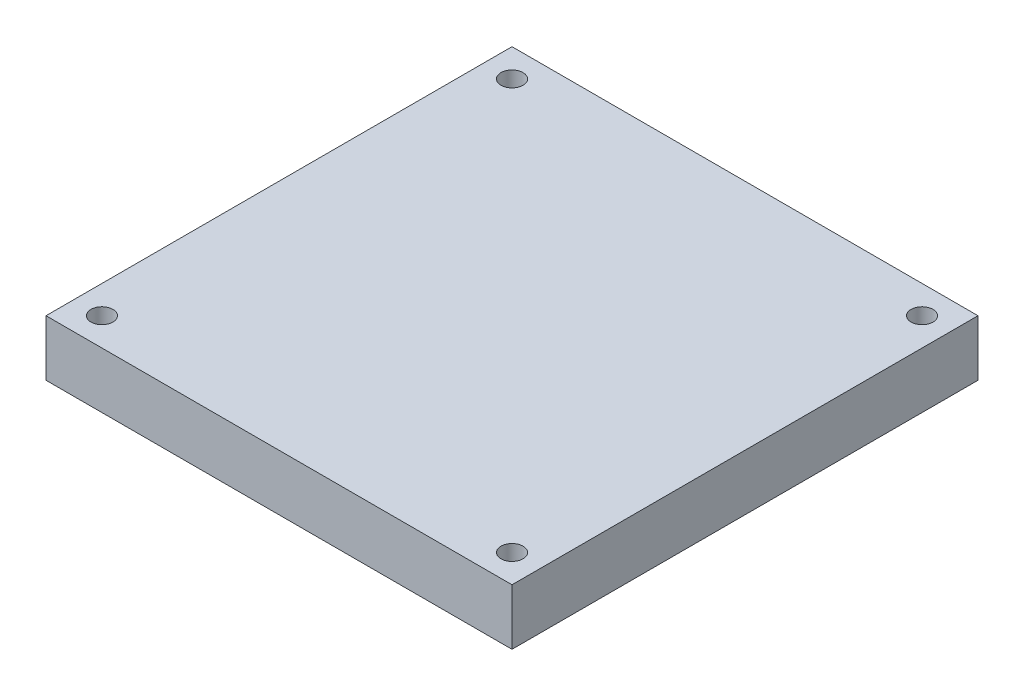
SolidWorks part; units mm, degrees
ref_plane "Front Plane" through (0, 0, 0) normal (0, 0, 1) x (1, 0, 0)
ref_plane "Top Plane" through (0, 0, 0) normal (0, 1, 0) x (1, 0, 0)
ref_plane "Right Plane" through (0, 0, 0) normal (1, 0, 0) x (0, 0, -1)
sketch "Sketch1" plane through (0, 0, 0) normal (0, 1, 0) x (1, 0, 0)
  line L1 (-31.75, -31.75) -> (31.75, -31.75)
  line L2 (-31.75, -31.75) -> (-31.75, 31.75)
  line L3 (-31.75, 31.75) -> (31.75, 31.75)
  line L4 (31.75, -31.75) -> (31.75, 31.75)
  line L5 (-31.75, -31.75) -> (31.75, 31.75) construction
  line L6 (-31.75, 31.75) -> (31.75, -31.75) construction
  point P0 (0, 0)
  dimension "D1" = 63.5
  dimension "D2" = 63.5
extrude "Boss-Extrude1" add sketch "Sketch1" along normal blind 7.62
hole_wizard "Ø3.0mm Dowel Hole1" positions "Sketch3" profile "Sketch4" hole size "Ø3.0" standard "ANSI Metric" end condition up to next
sketch "Sketch3" plane through (0, 0, 0) normal (0, -1, 0) x (-1, 0, 0)
  line L0 (-31.75, -31.75) -> (-31.75, 31.75) construction
  line L1 (31.75, -31.75) -> (-31.75, -31.75) construction
  point P0 (-27.94, -27.94)
  dimension "D1" = 3.81
  dimension "D2" = 3.81
sketch "Sketch4" plane through (27.94, 0, 27.94) normal (1, 0, 0) x (0, 0, -1)
  line L0 (0, 0) -> (0, 7.62)
  line L1 (0, 7.62) -> (1.5, 7.62)
  line L2 (1.5, 7.62) -> (1.5, 0.025)
  line L3 (1.5, 0.025) -> (1.525, 0)
  line L5 (1.525, 0) -> (0, 0)
  line L6 (-1.5, 0.025) -> (-1.525, 0) construction
  line L11 (0, -6.35) -> (0, 107.95) construction
  dimension "Thru Hole Dia." = 3
  dimension "Thru Hole Depth" = 7.62
  dimension "Near C'Sink Dia." = 3.05
  dimension "Near C'Sink Angle" = 90
pattern_linear "LPattern1" count 2 spacing 55.88 along (0, 0, -1) count 2 spacing 55.88 along (-1, 0, 0) of "Ø3.0mm Dowel Hole1"
sketch "Sketch5" plane through (0, 0, 0) normal (0, -1, 0) x (1, 0, 0)
  line L0 (0, 45.72) -> (0, -45.72) construction
  line L1 (12.7, 45.72) -> (12.7, -45.72)
  line L2 (-12.7, 45.72) -> (-12.7, -45.72)
  arc A0 (12.7, 45.72) -> (-12.7, 45.72) centre (0, 45.72) ccw
  arc A1 (-12.7, -45.72) -> (12.7, -45.72) centre (0, -45.72) ccw
  point P2 (0, 0)
  dimension "D1" = 12.7
  dimension "D2" = 91.44
sketch "Sketch6" plane through (0, 0, 0) normal (0, -1, 0) x (1, 0, 0)
  circle A0 centre (0, 0) radius 12.7
  dimension "D1" = 25.4
extrude "Cut-Extrude1" cut sketch "Sketch6" against normal blind 6.35
